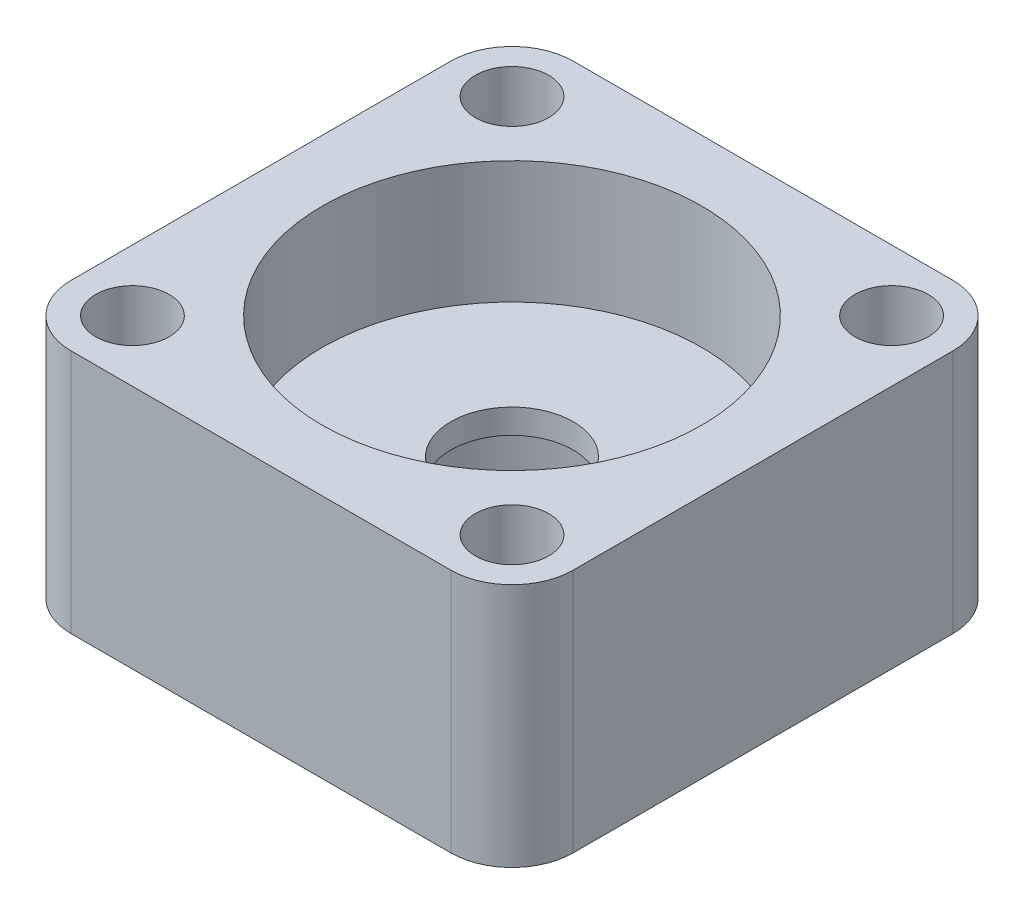
SolidWorks part; units mm, degrees
ref_plane "Front Plane" through (0, 0, 0) normal (0, 0, 1) x (1, 0, 0)
ref_plane "Top Plane" through (0, 0, 0) normal (0, 1, 0) x (1, 0, 0)
ref_plane "Right Plane" through (0, 0, 0) normal (1, 0, 0) x (0, 0, -1)
sketch "Sketch1" plane through (0, 0, 0) normal (0, 1, 0) x (1, 0, 0)
  line L1 (-15.5, 20.5) -> (15.5, 20.5)
  line L2 (-20.5, 15.5) -> (-20.5, -15.5)
  line L3 (-15.5, -20.5) -> (15.5, -20.5)
  line L4 (20.5, 15.5) -> (20.5, -15.5)
  circle A0 centre (0, 0) radius 11
  circle A1 centre (-15.5, 15.5) radius 1.75
  circle A2 centre (15.5, 15.5) radius 1.75
  circle A3 centre (15.5, -15.5) radius 1.75
  circle A4 centre (-15.5, -15.5) radius 1.75
  arc A5 (-15.5, 20.5) -> (-20.5, 15.5) centre (-15.5, 15.5) ccw
  arc A6 (20.5, 15.5) -> (15.5, 20.5) centre (15.5, 15.5) ccw
  arc A7 (15.5, -20.5) -> (20.5, -15.5) centre (15.5, -15.5) ccw
  arc A8 (-20.5, -15.5) -> (-15.5, -20.5) centre (-15.5, -15.5) ccw
  dimension "D1" = 3.5
  dimension "D2" = 31
  dimension "D3" = 31
  dimension "D4" = 15.5
  dimension "D5" = 15.5
  dimension "D6" = 5
  dimension "D7" = 5
  dimension "D8" = 5
  dimension "D9" = 5
  dimension "D10" = 22
extrude "Boss-Extrude1" add sketch "Sketch1" along normal blind 8
sketch "Sketch2" plane through (0, 8, 0) normal (0, 1, 0) x (1, 0, 0)
  line L4 (-20.5, 15.5) -> (-20.5, -15.5)
  line L5 (-15.5, -20.5) -> (15.5, -20.5)
  line L6 (20.5, -15.5) -> (20.5, 15.5)
  line L7 (15.5, 20.5) -> (-15.5, 20.5)
  line L8 (-20.5, 15.5) -> (-20.5, -15.5)
  line L9 (-15.5, -20.5) -> (15.5, -20.5)
  line L10 (20.5, -15.5) -> (20.5, 15.5)
  line L11 (15.5, 20.5) -> (-15.5, 20.5)
  circle A0 centre (-15.5, 15.5) radius 1.75 construction
  circle A1 centre (15.5, -15.5) radius 1.75 construction
  circle A2 centre (15.5, 15.5) radius 1.75 construction
  circle A3 centre (15.5, 15.5) radius 1.75
  arc A4 (-15.5, 20.5) -> (-20.5, 15.5) centre (-15.5, 15.5) ccw
  arc A5 (-20.5, -15.5) -> (-15.5, -20.5) centre (-15.5, -15.5) ccw
  arc A6 (15.5, -20.5) -> (20.5, -15.5) centre (15.5, -15.5) ccw
  arc A7 (20.5, 15.5) -> (15.5, 20.5) centre (15.5, 15.5) ccw
  arc A8 (-15.5, 20.5) -> (-20.5, 15.5) centre (-15.5, 15.5) ccw
  arc A9 (-20.5, -15.5) -> (-15.5, -20.5) centre (-15.5, -15.5) ccw
  arc A10 (15.5, -20.5) -> (20.5, -15.5) centre (15.5, -15.5) ccw
  arc A11 (20.5, 15.5) -> (15.5, 20.5) centre (15.5, 15.5) ccw
  circle A12 centre (15.5, -15.5) radius 1.75
  circle A13 centre (-15.5, 15.5) radius 1.75
  circle A14 centre (0, 0) radius 5
  circle A15 centre (-15.5, -15.5) radius 1.75
  dimension "D2" = 10
  dimension "D1" = 0
extrude "Boss-Extrude2" add sketch "Sketch2" along normal blind 2
sketch "Sketch3" plane through (0, 10, 0) normal (0, 1, 0) x (1, 0, 0)
  line L4 (-20.5, 15.5) -> (-20.5, -15.5)
  line L5 (-15.5, -20.5) -> (15.5, -20.5)
  line L6 (20.5, -15.5) -> (20.5, 15.5)
  line L7 (15.5, 20.5) -> (-15.5, 20.5)
  line L8 (-20.5, 15.5) -> (-20.5, -15.5)
  line L9 (-15.5, -20.5) -> (15.5, -20.5)
  line L10 (20.5, -15.5) -> (20.5, 15.5)
  line L11 (15.5, 20.5) -> (-15.5, 20.5)
  circle A0 centre (15.5, 15.5) radius 1.75 construction
  circle A1 centre (15.5, -15.5) radius 1.75 construction
  circle A2 centre (-15.5, -15.5) radius 1.75 construction
  circle A3 centre (-15.5, 15.5) radius 1.75 construction
  arc A4 (-15.5, 20.5) -> (-20.5, 15.5) centre (-15.5, 15.5) ccw
  arc A5 (-20.5, -15.5) -> (-15.5, -20.5) centre (-15.5, -15.5) ccw
  arc A6 (15.5, -20.5) -> (20.5, -15.5) centre (15.5, -15.5) ccw
  arc A7 (20.5, 15.5) -> (15.5, 20.5) centre (15.5, 15.5) ccw
  arc A8 (-15.5, 20.5) -> (-20.5, 15.5) centre (-15.5, 15.5) ccw
  arc A9 (-20.5, -15.5) -> (-15.5, -20.5) centre (-15.5, -15.5) ccw
  arc A10 (15.5, -20.5) -> (20.5, -15.5) centre (15.5, -15.5) ccw
  arc A11 (20.5, 15.5) -> (15.5, 20.5) centre (15.5, 15.5) ccw
  circle A12 centre (15.5, 15.5) radius 1.75
  circle A13 centre (15.5, -15.5) radius 1.75
  circle A14 centre (-15.5, -15.5) radius 1.75
  circle A15 centre (-15.5, 15.5) radius 1.75
  circle A16 centre (0, 0) radius 15.5
  dimension "D2" = 31
  dimension "D1" = 0
extrude "Boss-Extrude3" add sketch "Sketch3" along normal blind 10
sketch "Sketch4" plane through (0, 20, 0) normal (0, 1, 0) x (1, 0, 0)
  circle A0 centre (-15.5, 15.5) radius 3
  circle A1 centre (15.5, 15.5) radius 3
  circle A2 centre (15.5, -15.5) radius 3
  circle A3 centre (-15.5, -15.5) radius 3
  dimension "D1" = 6
extrude "Cut-Extrude1" cut sketch "Sketch4" against normal blind 15
